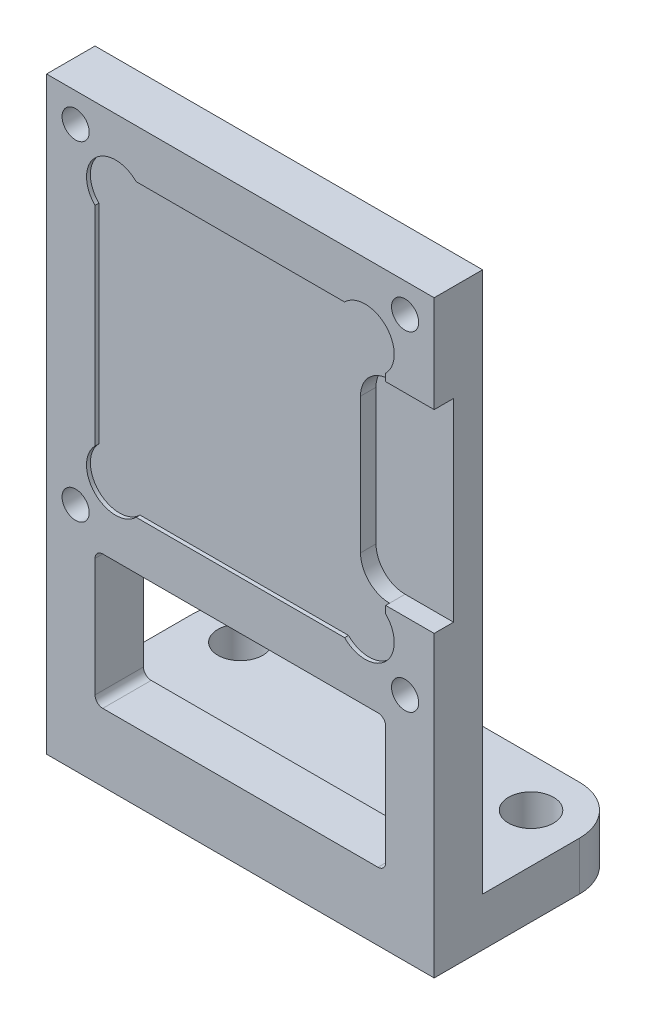
SolidWorks part; units mm, degrees
material "6061-T6 (SS)"
ref_plane "Front Plane" through (0, 0, 0) normal (0, 0, 1) x (1, 0, 0)
ref_plane "Top Plane" through (0, 0, 0) normal (0, 1, 0) x (1, 0, 0)
ref_plane "Right Plane" through (0, 0, 0) normal (1, 0, 0) x (0, 0, -1)
sketch "Sketch1" plane through (0, 0, 0) normal (1, 0, 0) x (0, 0, -1)
  line L0 (0, 12.7) -> (0, -25.908)
  line L1 (0, -25.908) -> (12.7, -25.908)
  line L2 (12.7, -25.908) -> (12.7, -22.733)
  line L3 (12.7, -22.733) -> (3.175, -22.733)
  line L4 (3.175, -22.733) -> (3.175, 12.7)
  line L5 (3.175, 12.7) -> (0, 12.7)
  dimension "D1" = 25.908
  dimension "D2" = 3.175
  dimension "D3" = 12.7
  dimension "D4" = 12.7
extrude "Boss-Extrude1" add sketch "Sketch1" along normal mid plane 25.4
sketch "Sketch2" plane through (0, 0, 0) normal (0, 0, 1) x (1, 0, 0)
  line L1 (-9.525, 9.525) -> (9.525, 9.525)
  line L2 (-9.525, 9.525) -> (-9.525, -9.525)
  line L3 (-9.525, -9.525) -> (9.525, -9.525)
  line L4 (9.525, 9.525) -> (9.525, -9.525)
  line L5 (-9.525, 9.525) -> (9.525, -9.525) construction
  line L6 (-9.525, -9.525) -> (9.525, 9.525) construction
  point P0 (0, 0)
  dimension "D1" = 19.05
extrude "Cut-Extrude1" cut sketch "Sketch2" against normal blind 0.254
sketch "Sketch3" plane through (0, 0, 0) normal (0, 0, 1) x (1, 0, 0)
  line L0 (12.7, 12.7) -> (12.7, -25.908) construction
  line L1 (9.525, 6.35) -> (12.7, 6.35)
  line L2 (9.525, 6.35) -> (9.525, -6.35)
  line L3 (9.525, -6.35) -> (12.7, -6.35)
  line L4 (12.7, 6.35) -> (12.7, -6.35)
  line L5 (9.525, 6.35) -> (12.7, -6.35) construction
  line L6 (9.525, -6.35) -> (12.7, 6.35) construction
  line L7 (9.525, -9.525) -> (9.525, 9.525) construction
  point P0 (11.1125, 0)
  dimension "D1" = 12.7
extrude "Cut-Extrude2" cut sketch "Sketch3" against normal blind 1.27
sketch "Sketch4" plane through (0, 0, 0) normal (0, 0, 1) x (1, 0, 0)
  line L0 (9.525, 9.525) -> (6.8309, 9.525) construction
  line L1 (9.525, 9.525) -> (9.525, 6.8309) construction
  line L2 (9.525, 6.35) -> (9.525, 9.525) construction
  line L3 (9.525, 9.525) -> (-9.525, 9.525) construction
  circle A0 centre (8.178, 8.178) radius 1.905
  dimension "D1" = 3.81
extrude "Cut-Extrude3" cut sketch "Sketch4" against normal up to surface (0.254 mm away) up to face at (3.175, 0, -0.254)
mirror "Mirror1" about plane through (0, 0, 0) normal (1, 0, 0) of "Cut-Extrude3"
mirror "Mirror2" about plane through (0, 0, 0) normal (0, 1, 0) of "Cut-Extrude3", "Mirror1"
sketch "Sketch5" plane through (0, 0, -0.254) normal (0, 0, 1) x (1, 0, 0)
  line L0 (9.525, 6.35) -> (9.525, -6.35) construction
  line L1 (12.7, 6.35) -> (9.525, 6.35) construction
  line L2 (9.525, -6.35) -> (12.7, -6.35) construction
  line L3 (7.62, 4.445) -> (7.62, -4.445)
  line L4 (9.525, -6.35) -> (9.525, 6.35) construction
  line L5 (9.525, -6.35) -> (9.525, 6.35)
  arc A0 (9.525, 6.35) -> (7.62, 4.445) centre (9.525, 4.445) ccw
  arc A1 (9.525, 6.8309) -> (6.8309, 9.525) centre (8.178, 8.178) ccw construction
  arc A2 (7.62, -4.445) -> (9.525, -6.35) centre (9.525, -4.445) ccw
extrude "Cut-Extrude4" cut sketch "Sketch5" against normal up to surface (1.016 mm away) up to face at (11.1125, 0, -1.27)
fillet "Fillet1" radius 3.175 2 edges at (-12.7, -24.3205, -12.7) (12.7, -24.3205, -12.7)
hole_wizard "#2-56 Tapped Hole1" positions "Sketch6" profile "Sketch7" tap size "#2-56" standard "ANSI Inch" end condition through all
sketch "Sketch6" plane through (0, 0, 0) normal (0, 0, 1) x (1, 0, 0)
  line L0 (10.795, 10.795) -> (-10.795, -10.795)
  line L3 (10.795, -10.795) -> (-10.795, 10.795)
  point P0 (-10.795, 10.795)
  point P2 (10.795, 10.795)
  point P4 (10.795, -10.795)
  point P6 (-10.795, -10.795)
  dimension "D1" = 21.59
  dimension "D2" = 21.59
sketch "Sketch7" plane through (-10.795, 10.795, 0) normal (1, 0, 0) x (0, -1, 0)
  line L0 (0, 0) -> (0, 12.7)
  line L1 (0, 12.7) -> (0.889, 12.7)
  line L2 (0.889, 12.7) -> (0.889, 0)
  line L5 (0.889, 0) -> (0, 0)
  line L11 (0, -6.35) -> (0, 107.95) construction
  dimension "Thru Tap Drill Dia." = 1.778
  dimension "Thru Tap Drill Depth" = 12.7
cosmetic thread "Hole Thread1" parameters "D2"=2.1844
cosmetic thread "Hole Thread2" parameters "D2"=2.1844
cosmetic thread "Hole Thread3" parameters "D2"=2.1844
cosmetic thread "Hole Thread4" parameters "D2"=2.1844
sketch "Sketch8" plane through (0, 0, 0) normal (0, 0, 1) x (1, 0, 0)
  line L0 (12.7, -6.35) -> (12.7, -25.908) construction
  line L1 (-12.7, 12.7) -> (12.7, 12.7) construction
  line L2 (-12.7, 12.7) -> (-12.7, -12.7) construction
  line L3 (-9.525, -12.7) -> (7.122, -12.7) construction
  line L4 (12.7, 12.7) -> (12.7, -12.7) construction
  line L5 (12.7, -22.733) -> (-12.7, -22.733) construction
  line L6 (12.7, -22.733) -> (-12.7, -22.733) construction
  line L7 (-12.7, 12.7) -> (-12.7, -25.908) construction
  line L8 (-9.525, -12.7) -> (9.525, -12.7)
  line L9 (-9.525, -12.7) -> (-9.525, -21.463)
  line L10 (-9.525, -21.463) -> (9.525, -21.463)
  line L11 (9.525, -12.7) -> (9.525, -21.463)
  line L17 (9.525, -12.7) -> (12.7, -12.7) construction
  dimension "D1" = 3.175
  dimension "D2" = 3.175
  dimension "D3" = 1.27
extrude "Cut-Extrude5" cut sketch "Sketch8" against normal through all
fillet "Fillet2" radius 0.508 4 edges at (9.525, -21.463, -1.5875) (-9.525, -12.7, -1.5875) (9.525, -12.7, -1.5875) (-9.525, -21.463, -1.5875)
hole_wizard "#4 Clearance Hole1" positions "Sketch9" profile "Sketch10" hole size "#4" standard "ANSI Inch" end condition through all
sketch "Sketch9" plane through (0, -22.733, 0) normal (0, 1, 0) x (1, 0, 0)
  line L0 (-9.525, 9.525) -> (0, 0)
  line L1 (0, 0) -> (9.525, 9.525)
  line L3 (12.7, 0) -> (-12.7, 0) construction
  point P0 (-9.525, 9.525)
  point P2 (9.525, 9.525)
  dimension "D1" = 19.05
  dimension "D2" = 9.525
sketch "Sketch10" plane through (-9.525, -22.733, -9.525) normal (1, 0, 0) x (0, 0, 1)
  line L0 (0, 0) -> (0, 3.175)
  line L1 (0, 3.175) -> (1.4732, 3.175)
  line L2 (1.4732, 3.175) -> (1.4732, 0)
  line L5 (1.4732, 0) -> (0, 0)
  line L11 (0, -6.35) -> (0, 107.95) construction
  dimension "Thru Hole Dia." = 2.9464
  dimension "Thru Hole Depth" = 3.175
